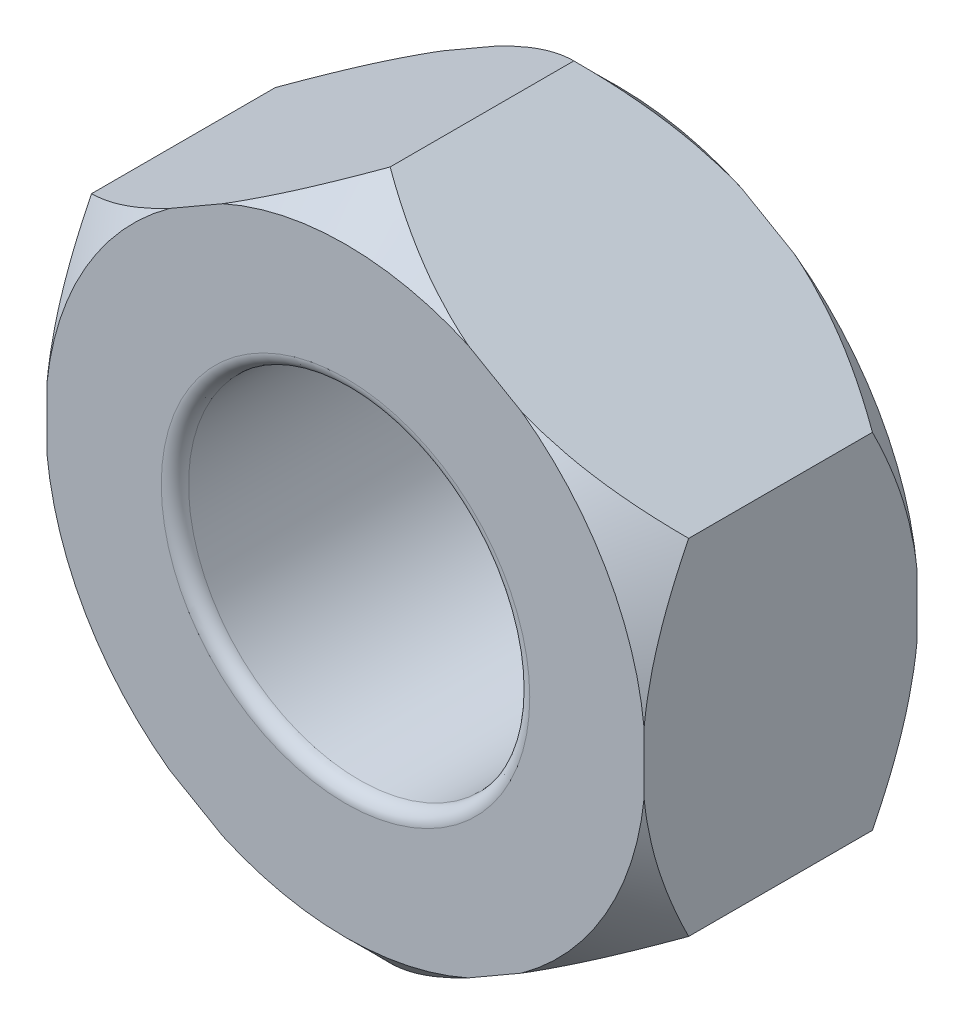
SolidWorks part; units mm, degrees
ref_plane "前视基准面" through (0, 0, 0) normal (0, 0, 1) x (1, 0, 0)
ref_plane "上视基准面" through (0, 0, 0) normal (0, 1, 0) x (1, 0, 0)
ref_plane "右视基准面" through (0, 0, 0) normal (1, 0, 0) x (0, 0, -1)
sketch "草图1" plane through (0, 0, 0) normal (0, 0, 1) x (1, 0, 0)
  line L1 (0, 4.0415) -> (-3.5, 2.0207)
  line L2 (-3.5, 2.0207) -> (-3.5, -2.0207)
  line L3 (-3.5, -2.0207) -> (0, -4.0415)
  line L4 (0, -4.0415) -> (3.5, -2.0207)
  line L5 (3.5, -2.0207) -> (3.5, 2.0207)
  line L6 (3.5, 2.0207) -> (0, 4.0415)
  circle A0 centre (0, 0) radius 3.5 construction
  dimension "D1" = 7
extrude "凸台-拉伸1" add sketch "草图1" along normal blind 3.2
sketch "草图2" plane through (0, 0, 0) normal (0, 0, -1) x (-1, 0, 0)
  circle A0 centre (0, 0) radius 2
extrude "切除-拉伸1" cut sketch "草图2" against normal blind 3.2
sketch "草图4" plane through (0, 0, 0) normal (1, 0, 0) x (0, 0, -1)
  line L0 (-2.677, 4.0415) -> (-3.2, 3.5185)
  line L1 (-3.2, 4.0415) -> (0, 4.0415) construction
  line L2 (-3.2, 2.0207) -> (-3.2, 4.0415) construction
  line L3 (-3.2, 3.5185) -> (-3.2, 4.0415)
  line L4 (-3.2, 4.0415) -> (-2.677, 4.0415)
  line L5 (0, 4.0415) -> (-0.523, 4.0415)
  line L6 (-0.523, 4.0415) -> (0, 3.5185)
  line L7 (0, 2.0207) -> (0, 4.0415) construction
  line L8 (0, 3.5185) -> (0, 4.0415)
  line L9 (0, 0) -> (-4.2303, 0) construction
  line L10 (0, -2.0207) -> (0, 2.0207) construction
revolve "切除-旋转1" cut sketch "草图4" angle 360 about L9
fillet "圆角1" radius 0.16 2 edges at (-2, 0, 3.2) (-2, 0, 0)
